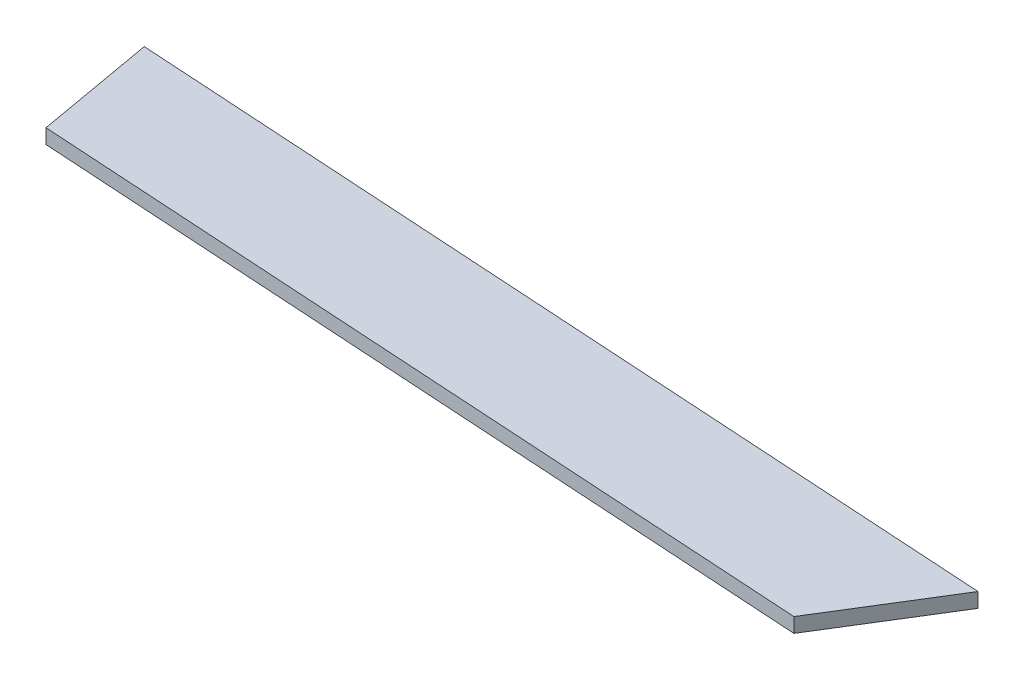
SolidWorks part; units mm, degrees
ref_plane "Plan de face" through (0, 0, 0) normal (0, 0, 1) x (1, 0, 0)
ref_plane "Plan de dessus" through (0, 0, 0) normal (0, 1, 0) x (1, 0, 0)
ref_plane "Plan de droite" through (0, 0, 0) normal (1, 0, 0) x (0, 0, -1)
sketch "Esquisse1" plane through (0, 0, 0) normal (0, 1, 0) x (1, 0, 0)
  line L0 (109.1812, -6.7635) -> (118.8151, 8.8114)
  line L1 (118.8151, 8.8114) -> (-2.8969, 16.3511)
  line L2 (-2.8969, 16.3511) -> (0, 0)
  line L3 (0, 0) -> (109.1812, -6.7635)
  point P4 (0, 0)
extrude "Boss.-Extru.1" add sketch "Esquisse1" along normal blind 2
